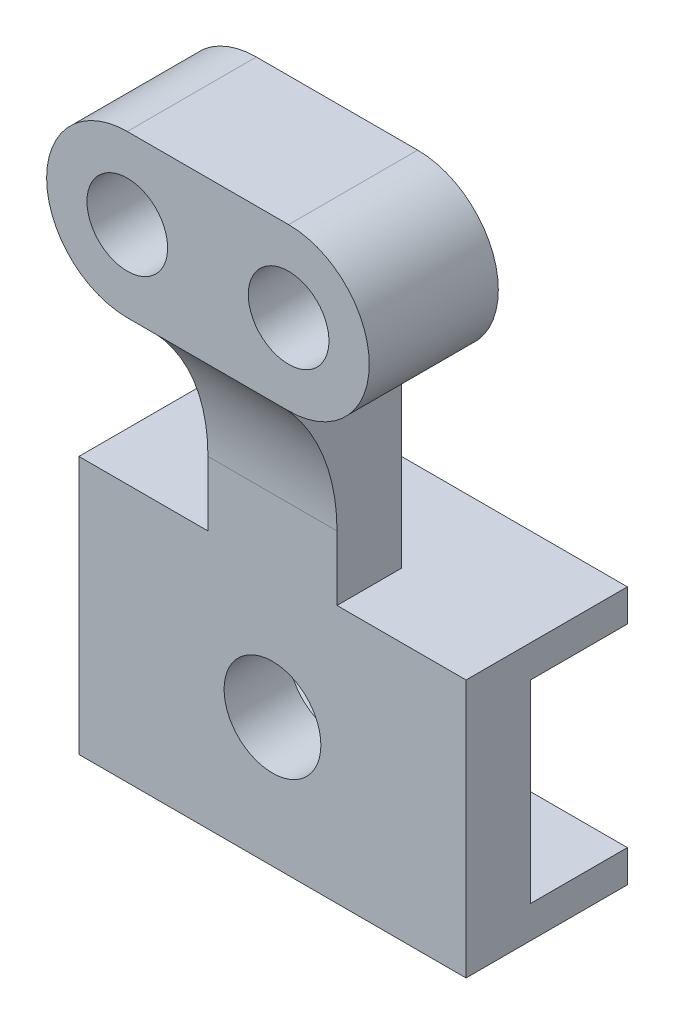
SolidWorks part; units mm, degrees
material "Plain Carbon Steel"
ref_plane "Front Plane" through (0, 0, 0) normal (1, 0, 0) x (0, 1, 0)
ref_plane "Top Plane" through (0, 0, 0) normal (0, 0, 1) x (0, 1, 0)
ref_plane "Right Plane" through (0, 0, 0) normal (0, 1, 0) x (-1, 0, 0)
sketch "Sketch1" plane through (0, 0, 0) normal (1, 0, 0) x (0, 1, 0)
  line L0 (0, 0) -> (0, 31.75)
  line L1 (0, 31.75) -> (-50.8, 31.75)
  line L2 (-50.8, 31.75) -> (-50.8, 0)
  line L3 (-50.8, 0) -> (-44.45, 0)
  line L4 (-44.45, 0) -> (-44.45, 19.05)
  line L5 (-44.45, 19.05) -> (-6.35, 19.05)
  line L6 (-6.35, 19.05) -> (-6.35, 0)
  line L7 (-6.35, 0) -> (0, 0)
  dimension "D1" = 6.35
  dimension "D2" = 31.75
  dimension "D3" = 12.7
  dimension "D4" = 50.8
  dimension "D5" = 6.35
extrude "Boss-Extrude1" add sketch "Sketch1" along normal mid plane 76.2
sketch "Sketch2" plane through (0, 0, 31.75) normal (0, 0, 1) x (1, 0, 0)
  line L0 (38.1, -50.8) -> (-38.1, -50.8) construction
  circle A0 centre (0, -25.4) radius 9.525
  dimension "D1" = 19.05
  dimension "D2" = 25.4
extrude "Cut-Extrude1" cut sketch "Sketch2" against normal through all both and the other way through all
sketch "Sketch3" plane through (0, 0, 0) normal (1, 0, 0) x (0, 1, 0)
  line L0 (0, 19.05) -> (41.0981, 19.05)
  line L4 (12.7, 31.75) -> (0, 31.75)
  line L5 (0, 31.75) -> (0, 19.05)
  line L6 (0, 0) -> (0, 31.75) construction
  line L7 (0, 31.75) -> (-50.8, 31.75) construction
  line L8 (-44.45, 19.05) -> (-6.35, 19.05) construction
  line L9 (41.0981, 44.45) -> (41.0981, 19.05)
  line L10 (-6.35, 0) -> (0, 0) construction
  arc A0 (41.0981, 44.45) -> (12.7, 31.75) centre (12.7, 69.85) cw
  dimension "D1" = 38.1
  dimension "D2" = 44.45
  dimension "D3" = 12.7
extrude "Boss-Extrude2" add sketch "Sketch3" along normal mid plane 25.4
sketch "Sketch4" plane through (0, 0, 19.05) normal (0, 0, -1) x (1, 0, 0)
  line L0 (-15.875, -56.9731) -> (15.875, -56.9731) construction
  line L1 (0, 0) -> (0, -113.9461) construction
  line L2 (-15.875, -41.0981) -> (15.875, -41.0981)
  line L3 (-15.875, -72.8481) -> (15.875, -72.8481)
  line L4 (12.7, -41.0981) -> (-12.7, -41.0981) construction
  arc A0 (-15.875, -41.0981) -> (-15.875, -72.8481) centre (-15.875, -56.9731) ccw
  arc A1 (15.875, -72.8481) -> (15.875, -41.0981) centre (15.875, -56.9731) ccw
  circle A2 centre (15.875, -56.9731) radius 7.9375
  circle A3 centre (-15.875, -56.9731) radius 7.9375
  point P4 (0, -56.9731)
  dimension "D3" = 15.875
  dimension "D4" = 15.875
  dimension "D1" = 31.75
  dimension "D2" = 31.75
extrude "Boss-Extrude3" add sketch "Sketch4" against normal blind 25.4
